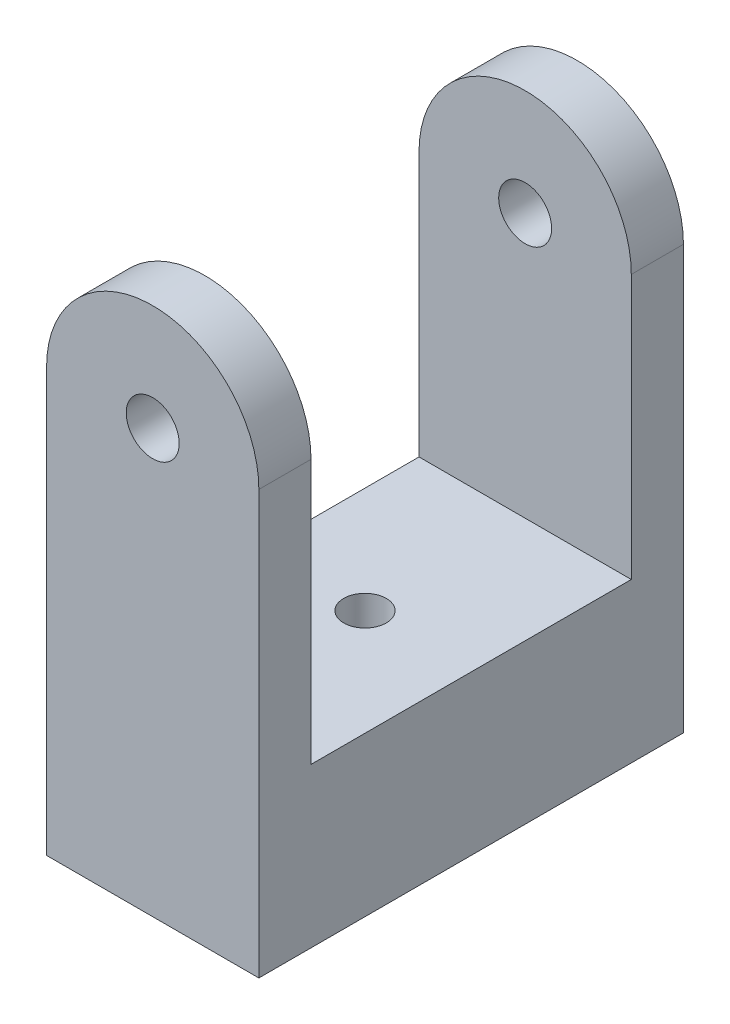
SolidWorks part; units mm, degrees
material "1060 Alloy"
ref_plane "Front Plane" through (0, 0, 0) normal (0, 0, 1) x (1, 0, 0)
ref_plane "Top Plane" through (0, 0, 0) normal (0, 1, 0) x (1, 0, 0)
ref_plane "Right Plane" through (0, 0, 0) normal (1, 0, 0) x (0, 0, -1)
sketch "Sketch3" plane through (0, 0, 0) normal (0, 0, 1) x (1, 0, 0)
  line L0 (-17.0099, -36.7199) -> (8.4401, -36.7199)
  line L1 (8.4401, -36.7199) -> (8.4401, 14.0051)
  line L3 (-17.0099, 14.0051) -> (-17.0099, -36.7199)
  circle A0 centre (-4.2849, 14.0051) radius 3.175
  arc A1 (8.4401, 14.0051) -> (-17.0099, 14.0051) centre (-4.2849, 14.0051) ccw
extrude "Boss-Extrude2" add sketch "Sketch3" along normal blind 50.9
sketch "Sketch7" plane through (8.4401, 0, 0) normal (1, 0, 0) x (0, 0, -1)
  line L0 (0, 26.7301) -> (-50.9, 26.7301) construction
  line L1 (-44.65, 26.7301) -> (-6.25, 26.7301)
  line L2 (-44.65, 26.7301) -> (-44.65, -17.6699)
  line L3 (-44.65, -17.6699) -> (-6.25, -17.6699)
  line L4 (-6.25, 26.7301) -> (-6.25, -17.6699)
  line L5 (-44.65, -17.6699) -> (-50.9, -17.6699) construction
  line L6 (-50.9, -36.7199) -> (-50.9, 14.0051) construction
  line L7 (-6.25, -17.6699) -> (0, -17.6699) construction
  line L8 (0, -36.7199) -> (0, 14.0051) construction
  dimension "D1" = 38.4
  dimension "D2" = 44.4
extrude "Cut-Extrude1" cut sketch "Sketch7" against normal through all
sketch "Sketch8" plane through (0, -36.7199, 0) normal (0, -1, 0) x (1, 0, 0)
  line L0 (-17.0099, 0) -> (8.4401, 50.9) construction
  line L1 (8.4401, 0) -> (-17.0099, 50.9) construction
  point P8 (-4.2849, 25.45)
hole_wizard "1/4-20 Tapped Hole1" positions "3DSketch1" profile "Sketch9" tap size "1/4-20" standard "ANSI Inch" end condition through all
sketch3d "3DSketch1"
  point P0 (-4.2849, -36.7199, 25.45)
cosmetic thread "Hole Thread1" parameters "D2"=6.35
sketch "Sketch9" plane through (-4.2849, -36.7199, 25.45) normal (1, 0, 0) x (0, 0, -1)
  line L0 (0, 0) -> (0, 63.45)
  line L1 (0, 63.45) -> (2.5527, 63.45)
  line L2 (2.5527, 63.45) -> (2.5527, 0)
  line L5 (2.5527, 0) -> (0, 0)
  line L11 (0, -6.35) -> (0, 107.95) construction
  dimension "Thru Tap Drill Dia." = 5.1054
  dimension "Thru Tap Drill Depth" = 63.45
